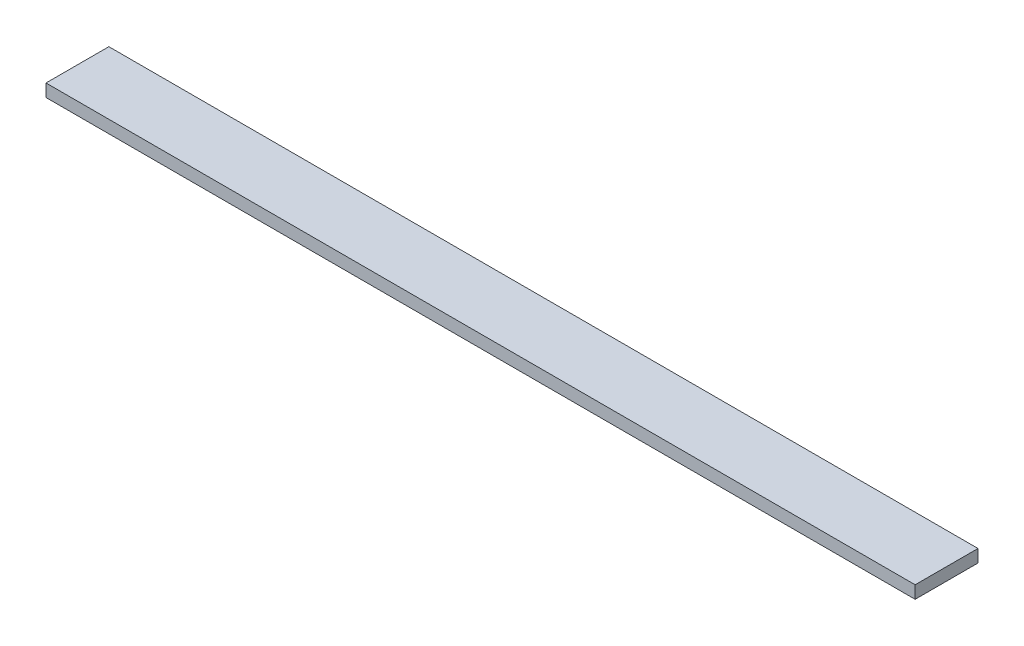
SolidWorks part; units mm, degrees
ref_plane "Front" through (0, 0, 0) normal (0, 0, 1) x (1, 0, 0)
ref_plane "Top" through (0, 0, 0) normal (0, 1, 0) x (1, 0, 0)
ref_plane "Right" through (0, 0, 0) normal (1, 0, 0) x (0, 0, -1)
sketch "Sketch1" plane through (0, 0, 0) normal (0, 1, 0) x (1, 0, 0)
  line L1 (0, 12.34) -> (341.217, 12.34)
  line L2 (0, 12.34) -> (0, -12.34)
  line L3 (0, -12.34) -> (341.217, -12.34)
  line L4 (341.217, 12.34) -> (341.217, -12.34)
  dimension "D1" = 24.68
  dimension "D2" = 341.217
extrude "Extrude1" add sketch "Sketch1" along normal mid plane 4.953
